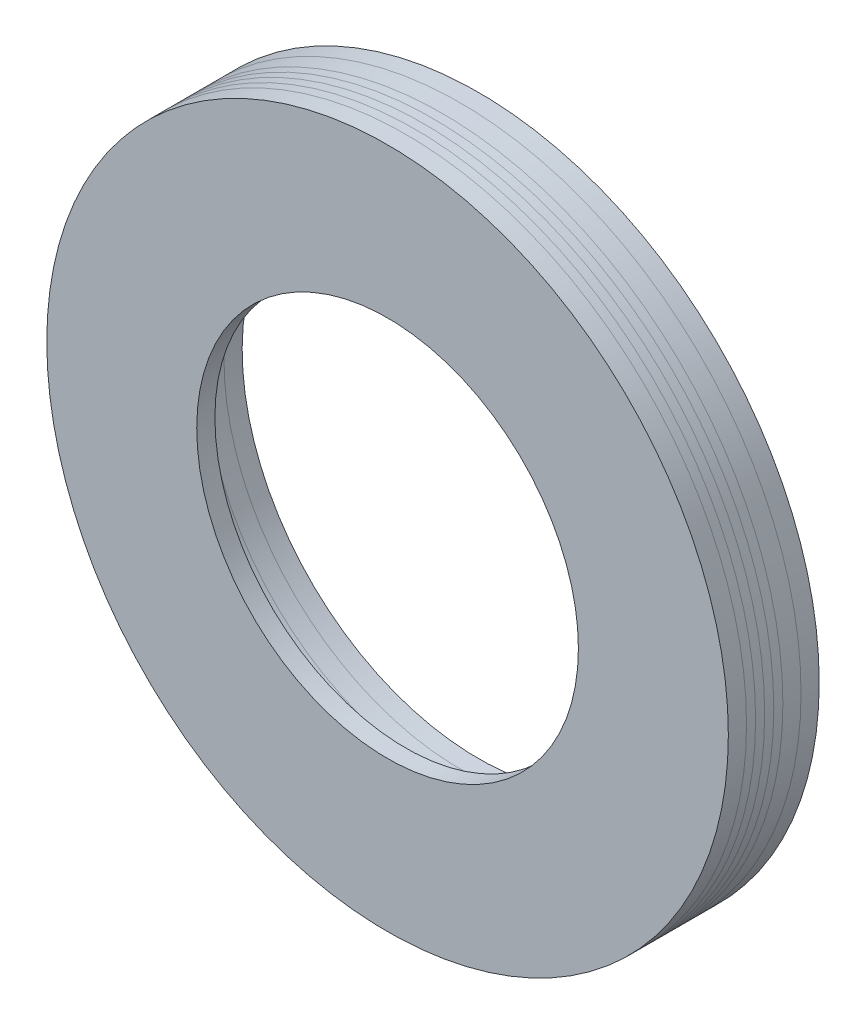
SolidWorks part; units mm, degrees
material "Ст 3 ГОСТ 380-2005"
ref_plane "Спереди" through (0, 0, 0) normal (0, 0, 1) x (1, 0, 0)
ref_plane "Сверху" through (0, 0, 0) normal (0, 1, 0) x (1, 0, 0)
ref_plane "Слева" through (0, 0, 0) normal (1, 0, 0) x (0, 0, -1)
sketch "Эскиз1" plane through (0, 0, 0) normal (0, 0, 1) x (1, 0, 0)
  line L0 (0, 16.5) -> (0, 0) construction
  line L1 (-4.5, 16.5) -> (4.5, 16.5)
  line L2 (-4.5, 16.5) -> (-4.5, 12.1963)
  line L4 (4.5, 16.5) -> (4.5, 12.1963)
  arc A0 (-4.5, 12.1963) -> (4.5, 12.1963) centre (0, 0) ccw
  circle A1 centre (0, 0) radius 18.75
  dimension "D1" = 26
  dimension "D4" = 37.5
  dimension "D5" = 1.6474
  dimension "D2" = 9
  dimension "D3" = 16.5
extrude "Вытянуть1" add sketch "Эскиз1" along normal blind 4
sketch "Эскиз2" plane through (0, 0, 0) normal (0, 1, 0) x (1, 0, 0)
  line L0 (-18.75, 0) -> (-18.75, -4) construction
  line L1 (-18.75, 0) -> (-18.75, -4)
  line L2 (18.75, -4) -> (18.75, 0) construction
  line L3 (18.75, -4) -> (18.75, 0)
  line L4 (-18.75, -1) -> (18.75, -1)
  line L5 (-18.75, -2) -> (18.75, -2)
  line L6 (-18.75, -2.5) -> (18.75, -2.5)
  line L7 (18.75, 0) -> (-18.75, 0) construction
  line L8 (-18.75, -3) -> (18.75, -3)
  line L9 (-18.75, -3.5) -> (18.75, -3.5)
  dimension "D1" = 1
  dimension "D2" = 1
  dimension "D3" = 0.5
  dimension "D4" = 0.5
  dimension "D5" = 0.5
split "Разделить1" trim tools "Эскиз2" resulting bodies 102 103 104 105 106 107
sketch "Эскиз3" plane through (0, 0, 4) normal (0, 0, 1) x (1, 0, 0)
  circle A0 centre (0, 0) radius 10.5
  circle A1 centre (0, 0) radius 18.75 construction
  circle A2 centre (0, 0) radius 18.75
  dimension "D1" = 21
extrude "Вытянуть2" add sketch "Эскиз3" along normal blind 1 separate body
